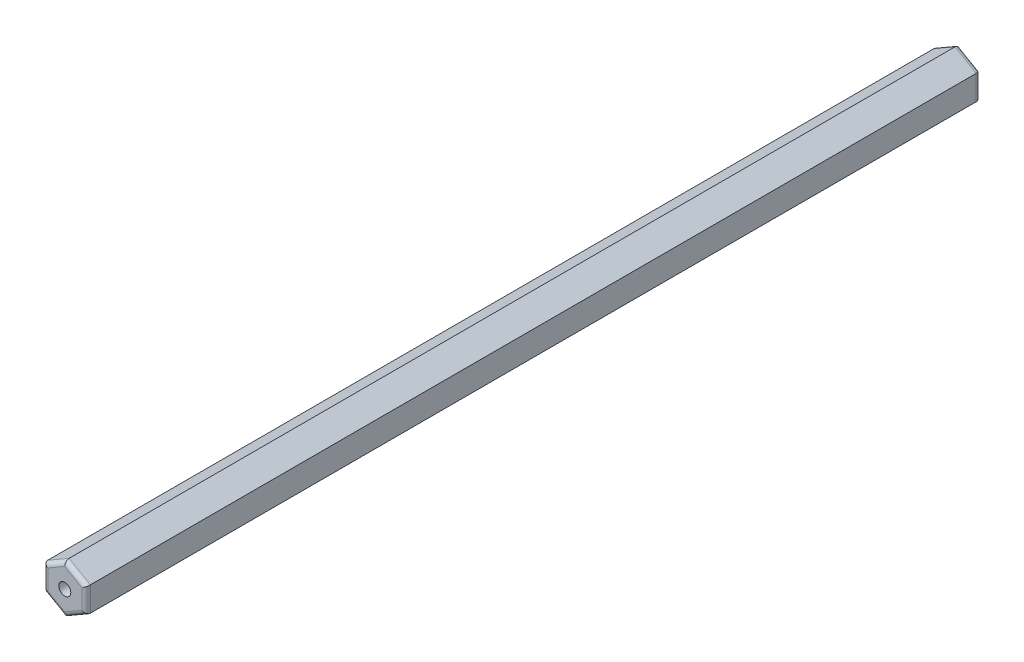
SolidWorks part; units mm, degrees
material "Inox rev"
ref_plane "Plano frontal" through (0, 0, 0) normal (0, 0, 1) x (1, 0, 0)
ref_plane "Plano superior" through (0, 0, 0) normal (0, 1, 0) x (1, 0, 0)
ref_plane "Plano direito" through (0, 0, 0) normal (1, 0, 0) x (0, 0, -1)
ref_plane "Plano1" through (0, 0, 135) normal (0, 0, 1) x (1, 0, 0)
sketch "Esboço1" plane through (0, 0, 135) normal (0, 0, 1) x (1, 0, 0)
  line L0 (-55.0021, 2.8868) -> (-57.5021, 1.4434)
  line L1 (-57.5021, 1.4434) -> (-57.5021, -1.4434)
  line L2 (-57.5021, -1.4434) -> (-55.0021, -2.8868)
  line L3 (-55.0021, -2.8868) -> (-52.5021, -1.4434)
  line L4 (-52.5021, -1.4434) -> (-52.5021, 1.4434)
  line L5 (-52.5021, 1.4434) -> (-55.0021, 2.8868)
  line L6 (-55.0021, 2.8868) -> (-55.0021, -2.8868) construction
  circle A0 centre (-55.0021, 0) radius 2.8868 construction
  dimension "D1" = 5
extrude "Ressalto-extrusão1" add sketch "Esboço1" against normal blind 105
fillet "Filete1" radius 0.5 12 edges at (-53.7521, -2.1651, 135) (-56.2521, -2.1651, 135) (-52.5021, 0, 135) (-57.5021, 0, 135) (-53.7521, 2.1651, 135) (-56.2521, 2.1651, 135) (-53.7521, -2.1651, 30) (-56.2521, -2.1651, 30) (-52.5021, 0, 30) (-57.5021, 0, 30) (-53.7521, 2.1651, 30) (-56.2521, 2.1651, 30)
sketch "Esboço2" plane through (0, 0, 135) normal (0, 0, 1) x (1, 0, 0)
  line L0 (-53.0021, -1.1547) -> (-53.0021, 1.1547) construction
  circle A0 centre (-55.0021, 0) radius 0.7015
  point P2 (-53.0021, 0)
extrude "Corte-extrusão1" cut sketch "Esboço2" against normal through all
